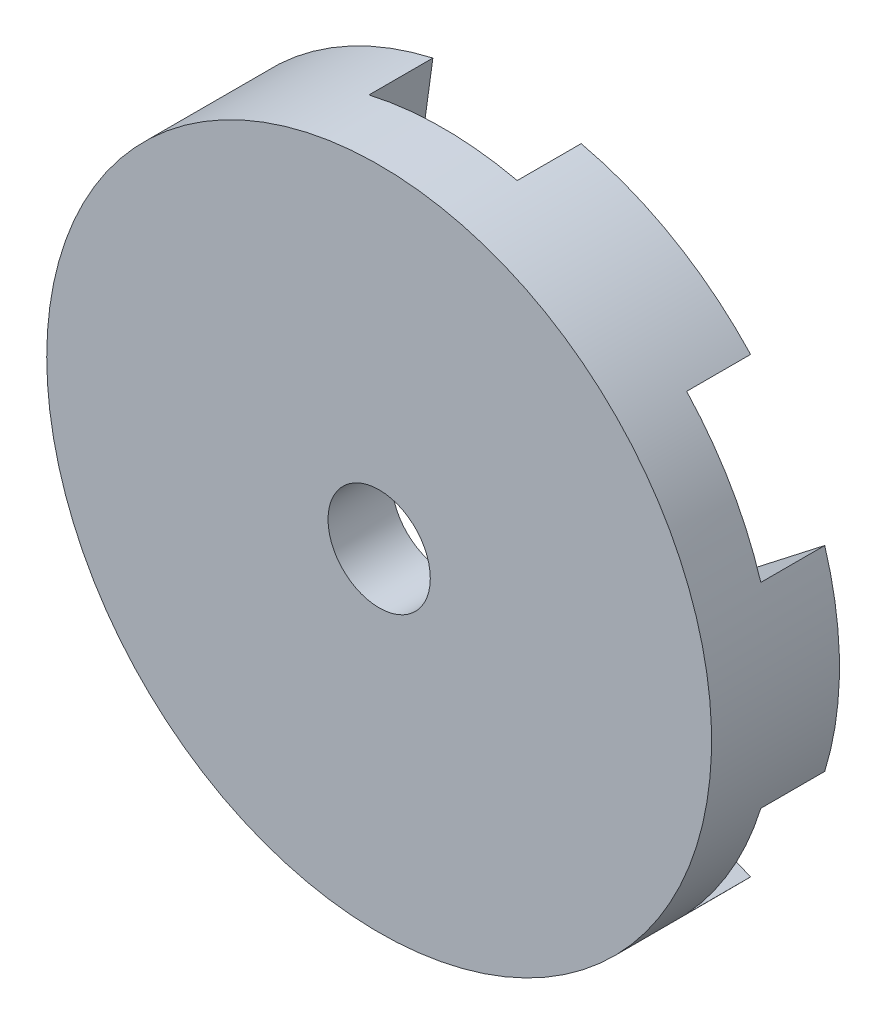
SolidWorks part; units mm, degrees
ref_plane "正面(Front)" through (0, 0, 0) normal (0, 0, 1) x (1, 0, 0)
ref_plane "平面(Top)" through (0, 0, 0) normal (0, 1, 0) x (1, 0, 0)
ref_plane "右側面(Right)" through (0, 0, 0) normal (1, 0, 0) x (0, 0, -1)
sketch "ｽｹｯﾁ1" plane through (0, 0, 0) normal (0, 0, 1) x (1, 0, 0)
  line L0 (0, 0) -> (0, 32.0386) construction
  line L1 (3.75, 6.4952) -> (2.7738, 13.5821)
  line L2 (0, 0) -> (3.75, 6.4952) construction
  arc A0 (2.7738, 13.5821) -> (0, 16) centre (0, 13.2) ccw
  dimension "D1" = 2.8
  dimension "D2" = 7.5
  dimension "D3" = 30
  dimension "D4" = 16
sketch "ｽｹｯﾁ2" plane through (0, 0, 0) normal (0, 0, 1) x (1, 0, 0)
  line L0 (3.75, 6.4952) -> (2.7738, 13.5821) construction
  line L1 (3.75, 6.4952) -> (2.7738, 13.5821)
  line L3 (0, 0) -> (0, 32.0386) construction
  line L4 (0, 0) -> (0, 32.0386) construction
  line L5 (-3.75, 6.4952) -> (-2.7738, 13.5821)
  line L6 (7.5, 0) -> (13.1493, 4.3889)
  line L7 (3.75, 6.4952) -> (10.3755, 9.1932)
  line L8 (3.75, -6.4952) -> (10.3755, -9.1932)
  line L9 (7.5, 0) -> (13.1493, -4.3889)
  line L10 (-3.75, -6.4952) -> (-2.7738, -13.5821)
  line L11 (3.75, -6.4952) -> (2.7738, -13.5821)
  line L12 (-7.5, 0) -> (-13.1493, -4.3889)
  line L13 (-3.75, -6.4952) -> (-10.3755, -9.1932)
  line L14 (-3.75, 6.4952) -> (-10.3755, 9.1932)
  line L15 (-7.5, 0) -> (-13.1493, 4.3889)
  line L16 (0, 0) -> (3.75, 6.4952) construction
  arc A0 (2.7738, 13.5821) -> (0, 16) centre (0, 13.2) ccw construction
  arc A1 (2.7738, 13.5821) -> (-2.7738, 13.5821) centre (0, 13.2) ccw
  arc A2 (13.1493, 4.3889) -> (10.3755, 9.1932) centre (11.4315, 6.6) ccw
  arc A3 (10.3755, -9.1932) -> (13.1493, -4.3889) centre (11.4315, -6.6) ccw
  arc A4 (-2.7738, -13.5821) -> (2.7738, -13.5821) centre (0, -13.2) ccw
  arc A5 (-13.1493, -4.3889) -> (-10.3755, -9.1932) centre (-11.4315, -6.6) ccw
  arc A6 (-10.3755, 9.1932) -> (-13.1493, 4.3889) centre (-11.4315, 6.6) ccw
  dimension "D2" = 7.5
  dimension "D3" = 30
  dimension "D1" = 6
sketch "ｽｹｯﾁ3" plane through (0, 0, 0) normal (0, 0, 1) x (1, 0, 0)
  circle A0 centre (0, 0) radius 13
  dimension "D1" = 26
extrude "ﾎﾞｽ - 押し出し1" add sketch "ｽｹｯﾁ3" along normal blind 5
extrude "ｶｯﾄ - 押し出し2" cut sketch "ｽｹｯﾁ2" along normal blind 2.5
sketch "ｽｹｯﾁ4" plane through (0, 0, 5) normal (0, 0, 1) x (1, 0, 0)
  circle A0 centre (0, 0) radius 10
  dimension "D1" = 20
sketch "ｽｹｯﾁ5" plane through (0, 0, 0) normal (0, 1, 0) x (1, 0, 0)
  line L0 (0, 0) -> (0, -21.9976) construction
  line L1 (0, -5) -> (25, -5)
  line L3 (25, -5) -> (25, -7)
  line L4 (25, -7) -> (10, -7)
  line L5 (10, -7) -> (10, -15)
  line L6 (10, -15) -> (25, -15)
  line L7 (25, -15) -> (25, -17)
  line L8 (25, -17) -> (0, -17)
  line L9 (0, -5) -> (0, -17)
  line L10 (-10, -5) -> (10, -5) construction
  dimension "D1" = 2
  dimension "D2" = 2
  dimension "D3" = 8
  dimension "D4" = 10
  dimension "D5" = 25
revolve "回転1" add sketch "ｽｹｯﾁ5" angle 360 about L0
sketch "ｽｹｯﾁ6" plane through (0, 0, 17) normal (0, 0, 1) x (1, 0, 0)
  circle A0 centre (0, 0) radius 2
  dimension "D1" = 4
extrude "ｶｯﾄ - 押し出し3" cut sketch "ｽｹｯﾁ6" against normal through all
sketch "ｽｹｯﾁ7" plane through (0, 0, 17) normal (0, 0, 1) x (1, 0, 0)
  circle A0 centre (0, 0) radius 7.5
  dimension "D1" = 15
extrude "ｶｯﾄ - 押し出し4" cut sketch "ｽｹｯﾁ7" against normal blind 8
sketch "ｽｹｯﾁ8" plane through (0, 0, 17) normal (0, 0, 1) x (1, 0, 0)
  line L0 (14.7902, 2.5) -> (9.6825, 2.5)
  line L1 (12.9904, 7.5) -> (6.6144, 7.5)
  line L2 (0, 0) -> (27.9307, 0) construction
  line L3 (14.7902, -2.5) -> (9.6825, -2.5)
  line L4 (12.9904, -7.5) -> (6.6144, -7.5)
  circle A0 centre (0, 0) radius 10 construction
  arc A1 (14.7902, 2.5) -> (12.9904, 7.5) centre (0, 0) ccw
  arc A2 (9.6825, 2.5) -> (6.6144, 7.5) centre (0, 0) ccw
  arc A3 (9.6825, -2.5) -> (6.6144, -7.5) centre (0, 0) cw
  arc A4 (14.7902, -2.5) -> (12.9904, -7.5) centre (0, 0) cw
  dimension "D1" = 20
  dimension "D4" = 5
  dimension "D2" = 5
  dimension "D3" = 5
extrude "ｶｯﾄ - 押し出し5" [suppressed] cut sketch "ｽｹｯﾁ8" against normal up to next contours A4 L3 A3 L4 | A2 L0 A1 L1
sketch "ｽｹｯﾁ9" plane through (0, 0, 15) normal (0, 0, -1) x (-1, 0, 0)
  line L0 (0, 0) -> (-20.5505, -24.4911) construction
  line L1 (0, 0) -> (0, -32.4809) construction
  line L2 (-3.8435, -0.6912) -> (-11.5569, -9.8837)
  line L3 (-3.8435, -0.6912) -> (-0.0133, -3.9051)
  line L4 (-11.5569, -9.8837) -> (-7.7267, -13.0976)
  line L5 (-0.0133, -3.9051) -> (-7.7267, -13.0976)
  line L6 (-3.8435, -0.6912) -> (-7.7267, -13.0976) construction
  line L7 (-11.5569, -9.8837) -> (-0.0133, -3.9051) construction
  point P5 (-5.7851, -6.8944)
  dimension "D1" = 40
  dimension "D2" = 5
  dimension "D3" = 12
  dimension "D4" = 3
extrude "ｶｯﾄ - 押し出し6" cut sketch "ｽｹｯﾁ9" along normal blind 5
mirror "ﾐﾗｰ1" about plane through (0, 0, 0) normal (1, 0, 0) of "ｶｯﾄ - 押し出し6"
fillet "ﾌｨﾚｯﾄ1" radius 1 2 edges at (4.3087, -9.0242, 12.5) (-4.3087, -9.0242, 12.5)
sketch "ｽｹｯﾁ10" plane through (0, 0, 17) normal (0, 0, 1) x (1, 0, 0)
  line L0 (0, 0) -> (0, 32.0386) construction
  line L1 (-1, 23) -> (1, 23)
  line L2 (-1, 23) -> (-1, 9.5)
  line L3 (-1, 9.5) -> (1, 9.5)
  line L4 (1, 23) -> (1, 9.5)
  line L5 (-1, 23) -> (1, 9.5) construction
  line L6 (-1, 9.5) -> (1, 23) construction
  circle A0 centre (0, 0) radius 25 construction
  circle A2 centre (0, 0) radius 7.5 construction
  point P0 (0, 16.25)
  dimension "D1" = 2
  dimension "D2" = 2
  dimension "D3" = 2
extrude "ｶｯﾄ - 押し出し7" cut sketch "ｽｹｯﾁ10" against normal blind 0.5
sketch "ｽｹｯﾁ11" plane through (0, 0, 5) normal (0, 0, -1) x (-1, 0, 0)
  circle A0 centre (0, 0) radius 25 construction
  circle A1 centre (0, 0) radius 25
extrude "ｶｯﾄ - 押し出し8" cut sketch "ｽｹｯﾁ11" against normal through all
